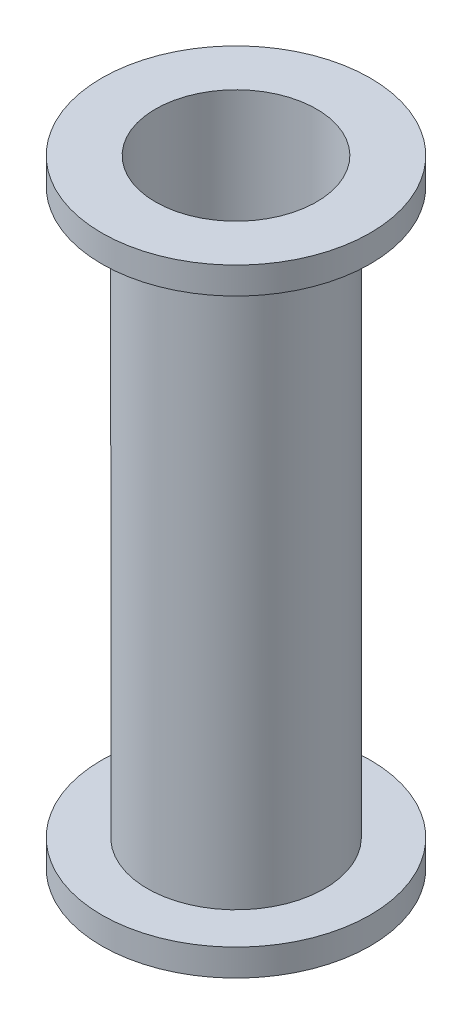
SolidWorks part; units mm, degrees
material "6061-T6 (SS)"
ref_plane "Front Plane" through (0, 0, 0) normal (0, 0, 1) x (1, 0, 0)
ref_plane "Top Plane" through (0, 0, 0) normal (0, 1, 0) x (1, 0, 0)
ref_plane "Right Plane" through (0, 0, 0) normal (1, 0, 0) x (0, 0, -1)
sketch "Sketch2" plane through (0, 0, 0) normal (0, 1, 0) x (1, 0, 0)
  circle A0 centre (0, 0) radius 38.1
  circle A1 centre (0, 0) radius 41.91
  dimension "D1" = 83.82
  dimension "D2" = 76.2
extrude "Base Cylinder" add sketch "Sketch2" along normal blind 292.1
sketch "Sketch3" plane through (0, 0, 0) normal (0, -1, 0) x (1, 0, 0)
  circle A0 centre (0, 0) radius 38.1
  circle A1 centre (0, 0) radius 63.5
  dimension "D1" = 127
extrude "Aft Flange" add sketch "Sketch3" against normal blind 12.7
sketch "Sketch4" plane through (0, 292.1, 0) normal (0, 1, 0) x (1, 0, 0)
  circle A0 centre (0, 0) radius 38.1
  circle A1 centre (0, 0) radius 63.5
  dimension "D1" = 127
extrude "Forward Flange" add sketch "Sketch4" against normal blind 12.7
fillet "Flange Fillet" [suppressed] radius 4.7625
sketch "Sketch6" plane through (0, 0, 0) normal (0, -1, 0) x (1, 0, 0)
  circle A0 centre (0, 0) radius 50.0761
  circle A1 centre (0, 0) radius 47.0027
  dimension "D1" = 100.1522
  dimension "D2" = 94.0054
extrude "Aft O-Ring" [suppressed] cut sketch "Sketch6" against normal blind 1.9812
sketch "Sketch7" plane through (0, 292.1, 0) normal (0, 1, 0) x (1, 0, 0)
  circle A0 centre (0, 0) radius 50.0761
  circle A1 centre (0, 0) radius 47.0027
  dimension "D1" = 100.1522
  dimension "D2" = 94.0054
extrude "Forward O-Ring" [suppressed] cut sketch "Sketch7" against normal blind 1.9812
sketch "Sketch For Bolt Holes" [suppressed] plane through (0, 0, 0) normal (0, -1, 0) x (1, 0, 0)
  circle A0 centre (-56.769, 0) radius 1.5875
  circle A1 centre (-49.1634, 28.3845) radius 1.5875
  circle A2 centre (-28.3845, 49.1634) radius 1.5875
  circle A3 centre (0, 56.769) radius 1.5875
  circle A4 centre (28.3845, 49.1634) radius 1.5875
  circle A5 centre (49.1634, 28.3845) radius 1.5875
  circle A6 centre (56.769, 0) radius 1.5875
  circle A7 centre (49.1634, -28.3845) radius 1.5875
  circle A8 centre (28.3845, -49.1634) radius 1.5875
  circle A9 centre (0, -56.769) radius 1.5875
  circle A10 centre (-28.3845, -49.1634) radius 1.5875
  circle A11 centre (-49.1634, -28.3845) radius 1.5875
  point P36 (0, 0)
  dimension "D2" = 3.175
  dimension "D1" = 56.769
  dimension "D3" = 12
hole_wizard "1/8 (0.125) Diameter Hole2" [suppressed] positions "Sketch8" profile "Sketch9" hole size "1/8" standard "ANSI Inch"
sketch "Sketch8" [suppressed] plane through (0, 0, 0) normal (0, -1, 0) x (-1, 0, 0)
  point P0 (-28.3845, -49.1634)
  point P3 (-49.1634, -28.3845)
  point P6 (-56.769, 0)
  point P9 (-49.1634, 28.3845)
  point P12 (-28.3845, 49.1634)
  point P15 (0, 56.769)
  point P18 (28.3845, 49.1634)
  point P21 (49.1634, 28.3845)
  point P24 (56.769, 0)
  point P27 (49.1634, -28.3845)
  point P30 (28.3845, -49.1634)
  point P33 (0, -56.769)
  point P36 (-28.3845, -49.1634)
  point P38 (-49.1634, -28.3845)
  point P40 (-56.769, 0)
sketch "Sketch9" plane through (28.3845, 0, 49.1634) normal (1, 0, 0) x (0, 0, -1)
  line L0 (0, 0) -> (0, 26.3539)
  line L1 (0, 26.3539) -> (1.5875, 25.4)
  line L2 (1.5875, 25.4) -> (1.5875, 0)
  line L5 (1.5875, 0) -> (0, 0)
  line L10 (0, 26.3539) -> (-1.5875, 25.4) construction
  line L11 (0, -6.35) -> (0, 107.95) construction
  dimension "Hole Dia." = 3.175
  dimension "Hole Depth" = 25.4
  dimension "Drill Angle" = 118
sketch "Dowel Hole Sketch" [suppressed] plane through (0, 0, 0) normal (0, -1, 0) x (1, 0, 0)
  line L0 (0, 0) -> (-56.769, 0) construction
  line L1 (0, 0) -> (-54.8346, -14.6929) construction
  line L2 (0, 0) -> (0, -56.769) construction
  line L3 (0, 0) -> (54.8346, 14.6929) construction
  circle A0 centre (0, 0) radius 56.769
  circle A1 centre (-54.8346, -14.6929) radius 4.6172
  circle A2 centre (54.8346, 14.6929) radius 3.4532
  dimension "D1" = 15
hole_wizard "1/4 (0.25) Press Dowel Hole1" [suppressed] positions "Sketch14" profile "Sketch12" hole size "1/4" standard "ANSI Inch"
sketch "Sketch14" [suppressed] plane through (0, 0, 0) normal (0, -1, 0) x (-1, 0, 0)
  point P0 (54.8346, 14.6929)
  point P3 (-54.8346, -14.6929)
sketch "Sketch12" plane through (-54.8346, 0, -14.6929) normal (1, 0, 0) x (0, 0, -1)
  line L0 (0, 0) -> (0, 8.2577)
  line L1 (0, 8.2577) -> (3.175, 6.35)
  line L2 (3.175, 6.35) -> (3.175, 0)
  line L5 (3.175, 0) -> (0, 0)
  line L10 (0, 8.2577) -> (-3.175, 6.35) construction
  line L11 (0, -6.35) -> (0, 107.95) construction
  dimension "Hole Dia." = 6.35
  dimension "Hole Depth" = 6.35
  dimension "Drill Angle" = 118
hole_wizard "1/8 (0.125) Diameter Hole4" [suppressed] positions "Sketch19" profile "Sketch21" hole size "1/8" standard "ANSI Inch"
sketch "Sketch19" [suppressed] plane through (0, 0, 0) normal (0, -1, 0) x (-1, 0, 0)
  point P0 (-54.8346, -14.6929)
  point P3 (54.8346, 14.6929)
sketch "Sketch21" plane through (54.8346, 0, 14.6929) normal (1, 0, 0) x (0, 0, -1)
  line L0 (0, 0) -> (0, 283.8423)
  line L1 (0, 283.8423) -> (1.5875, 283.8423)
  line L2 (1.5875, 283.8423) -> (1.5875, 0)
  line L5 (1.5875, 0) -> (0, 0)
  line L11 (0, -6.35) -> (0, 107.95) construction
  dimension "Thru Hole Dia." = 3.175
  dimension "Thru Hole Depth" = 283.8423
ref_plane "Hoop Mid-Plane" [suppressed] through (0, 146.05, 0) normal (0, 1, 0) x (1, 0, 0)
mirror "Forward Mirror BC and Pin" [suppressed] about plane through (0, 146.05, 0) normal (0, 1, 0)
ref_plane "PressureTapHolePlane" [suppressed] through (0, 0, 47.625) normal (0, 0, 1) x (1, 0, 0)
sketch "PressureTapHole" [suppressed] plane through (0, 0, 47.625) normal (0, 0, 1) x (1, 0, 0)
  line L1 (52.3875, 12.7) -> (-52.3875, 12.7) construction
  circle A0 centre (0, 31.75) radius 8.2246
  dimension "D1" = 19.05
hole_wizard "PressureTap1" [suppressed] positions "Sketch27" profile "Sketch28" legacy
sketch "Sketch27" [suppressed] plane through (0, 0, 47.625) normal (0, 0, 1) x (1, 0, 0)
  point P0 (0, 31.75)
sketch "Sketch28" plane through (0, 31.75, 47.625) normal (1, 0, 0) x (0, -1, 0)
  line L0 (0, 0) -> (0, 6.35)
  line L1 (0, 6.35) -> (0.3969, 6.35)
  line L2 (0.3969, 6.35) -> (0.3969, 1.5875)
  line L3 (0.3969, 1.5875) -> (1.5875, 1.5875)
  line L4 (1.5875, 1.5875) -> (1.5875, 0)
  line L5 (1.5875, 0) -> (0, 0)
  line L6 (0, 110) -> (0, -10) construction
  dimension "Diameter" = 0.7937
  dimension "Depth" = 6.35
  dimension "C-Bore Diameter" = 3.175
  dimension "C-Bore Depth" = 1.5875
ref_plane "PressureTapHole2Plane" [suppressed] through (0, 0, -47.625) normal (0, 0, 1) x (1, 0, 0)
sketch "PressureTapHole2" [suppressed] plane through (0, 0, -47.625) normal (0, 0, 1) x (1, 0, 0)
  line L0 (-52.3875, 279.4) -> (52.3875, 279.4) construction
  circle A0 centre (0, 254) radius 3.4964
  dimension "D1" = 25.4
hole_wizard "PressureTap2" [suppressed] positions "Sketch30" profile "Sketch31" legacy
sketch "Sketch30" [suppressed] plane through (0, 0, -47.625) normal (0, 0, 1) x (1, 0, 0)
  point P0 (0, 254)
sketch "Sketch31" plane through (0, 254, -47.625) normal (1, 0, 0) x (0, 1, 0)
  line L0 (0, 0) -> (0, 6.35)
  line L1 (0, 6.35) -> (0.7938, 6.35)
  line L2 (0.7938, 6.35) -> (0.7938, 3.175)
  line L3 (0.7938, 3.175) -> (1.5875, 3.175)
  line L4 (1.5875, 3.175) -> (1.5875, 0)
  line L5 (1.5875, 0) -> (0, 0)
  line L6 (0, 110) -> (0, -10) construction
  dimension "Diameter" = 1.5875
  dimension "Depth" = 6.35
  dimension "C-Bore Diameter" = 3.175
  dimension "C-Bore Depth" = 3.175
sketch "Sketch32" plane through (0, 292.1, 0) normal (0, 1, 0) x (1, 0, 0)
  line L0 (0, -69.85) -> (0, 69.85) construction
  line L1 (-64.2938, -36.7675) -> (-62.7062, -36.7675)
  line L2 (-64.2938, -36.7675) -> (-64.2938, 36.7675)
  line L3 (-64.2938, 36.7675) -> (-62.7062, 36.7675)
  line L4 (-62.7062, -36.7675) -> (-62.7062, 36.7675)
  line L5 (-64.2938, -36.7675) -> (-62.7062, 36.7675) construction
  line L6 (-64.2938, 36.7675) -> (-62.7062, -36.7675) construction
  line L7 (64.2938, 36.7675) -> (62.7062, 36.7675)
  line L8 (62.7062, -36.7675) -> (62.7062, 36.7675)
  line L9 (64.2938, -36.7675) -> (62.7062, -36.7675)
  line L10 (64.2938, -36.7675) -> (64.2938, 36.7675)
  circle A0 centre (0, 0) radius 63.5 construction
  point P0 (-63.5, 0)
  dimension "D1" = 1.5875
extrude "MillGrips" [suppressed] cut sketch "Sketch32" against normal through all both and the other way through all
